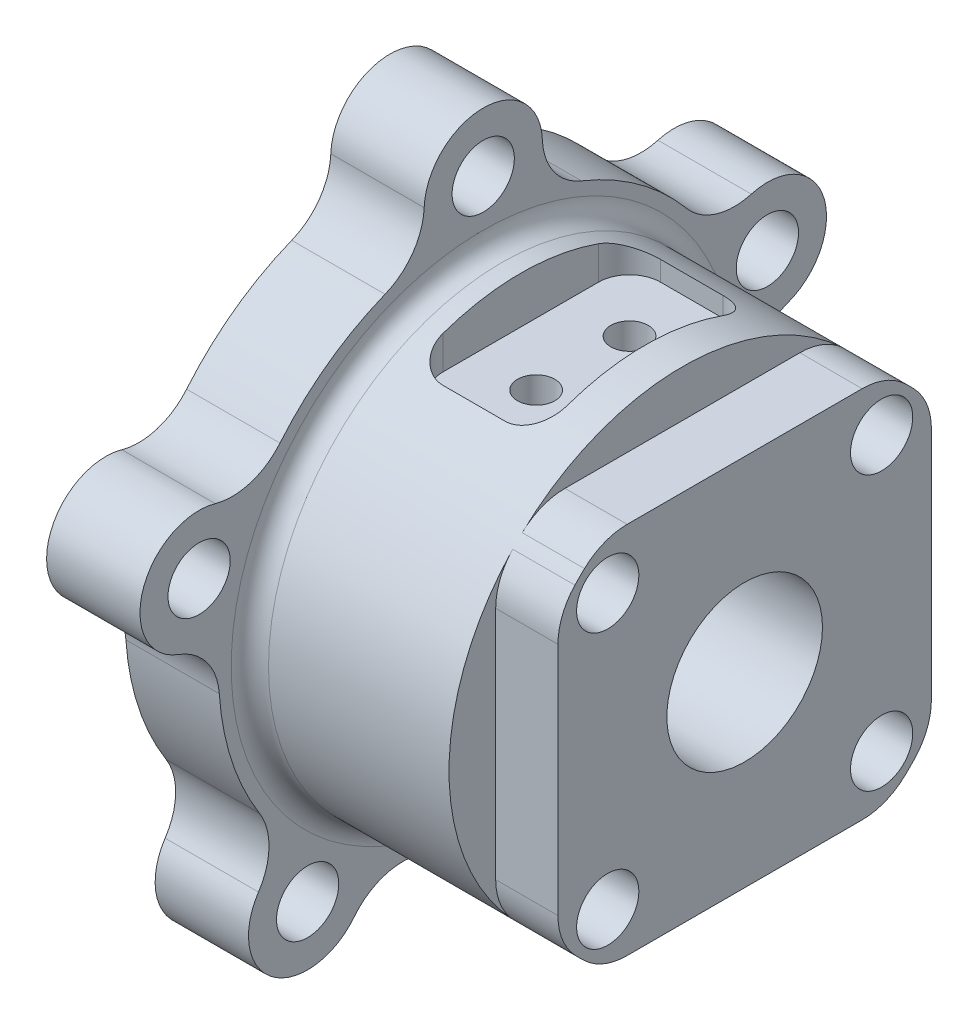
SolidWorks part; units mm, degrees
material "Plain Carbon Steel"
ref_plane "Front Plane" through (0, 0, 0) normal (0, 0, 1) x (1, 0, 0)
ref_plane "Top Plane" through (0, 0, 0) normal (0, 1, 0) x (1, 0, 0)
ref_plane "Right Plane" through (0, 0, 0) normal (1, 0, 0) x (0, 0, -1)
sketch "Sketch1" plane through (0, 0, 0) normal (0, 0, 1) x (1, 0, 0)
  line L0 (0, 0) -> (-104.2903, 0) construction
  line L1 (0, 0) -> (0, 37.5)
  line L2 (0, 37.5) -> (-42, 37.5)
  line L3 (-42, 37.5) -> (-42, 57.5)
  line L4 (-42, 57.5) -> (-57, 57.5)
  line L5 (-57, 57.5) -> (-57, 0)
  line L6 (-57, 0) -> (0, 0)
  dimension "D1" = 75
  dimension "D2" = 115
  dimension "D3" = 42
  dimension "D4" = 15
revolve "Revolve1" add sketch "Sketch1" angle 360 about L0
sketch "Sketch2" plane through (0, 0, 0) normal (1, 0, 0) x (0, 0, -1)
  line L1 (30, -30) -> (-30, -30)
  line L2 (30, -30) -> (30, 30)
  line L3 (30, 30) -> (-30, 30)
  line L4 (-30, -30) -> (-30, 30)
  line L5 (30, -30) -> (-30, 30) construction
  line L6 (30, 30) -> (-30, -30) construction
  circle A1 centre (0, 0) radius 48.1344
  point P0 (0, 0)
  dimension "D1" = 60
extrude "Cut-Extrude1" cut sketch "Sketch2" against normal blind 10
fillet "Fillet1" radius 10 8 edges at (-5, 30, 22.5) (-5, 30, -22.5) (-5, 22.5, -30) (-5, -22.5, -30) (-5, -30, -22.5) (-5, -30, 22.5) (-5, -22.5, 30) (-5, 22.5, 30)
hole_wizard "Ø10.0mm Dowel Hole2" positions "Sketch3" profile "Sketch4" hole size "Ø10.0" standard "ANSI Metric" end condition through all
sketch "Sketch3" plane through (0, 0, 0) normal (1, 0, 0) x (0, 0, -1)
  line L0 (30, -18.8746) -> (30, 18.8746) construction
  line L1 (-30, 18.8746) -> (-30, -18.8746) construction
  line L2 (18.8746, 30) -> (-18.8746, 30) construction
  line L3 (-18.8746, -30) -> (18.8746, -30) construction
  point P0 (22, 22)
  point P3 (-22, 22)
  point P6 (-22, -22)
  point P9 (22, -22)
  dimension "D1" = 8
  dimension "D2" = 8
  dimension "D3" = 8
  dimension "D4" = 8
sketch "Sketch4" plane through (0, 22, -22) normal (0, 1, 0) x (0, 0, -1)
  line L0 (0, 0) -> (0, 57)
  line L1 (0, 57) -> (5, 57)
  line L2 (5, 57) -> (5, 0)
  line L5 (5, 0) -> (0, 0)
  line L11 (0, -6.35) -> (0, 107.95) construction
  dimension "Thru Hole Dia." = 10
  dimension "Thru Hole Depth" = 57
sketch "Sketch5" plane through (0, 0, 0) normal (0, 1, 0) x (1, 0, 0)
  line L0 (0, 0) -> (-16, 0) construction
  line L1 (-36, 17.5) -> (-16, 17.5)
  line L2 (-36, 17.5) -> (-36, -17.5)
  line L3 (-36, -17.5) -> (-16, -17.5)
  line L4 (-16, 17.5) -> (-16, -17.5)
  line L5 (-10, -37.5) -> (-10, 37.5) construction
  line L6 (-42, -57.5) -> (-42, 57.5) construction
  dimension "D1" = 6
  dimension "D2" = 6
  dimension "D3" = 35
extrude "Cut-Extrude2" cut sketch "Sketch5" along normal through all from offset 30
fillet "Fillet2" radius 5 4 edges at (-16, 31.5831, 17.5) (-16, 31.5831, -17.5) (-36, 31.5831, 17.5) (-36, 31.5831, -17.5)
hole_wizard "Ø6.0mm Dowel Hole1" positions "Sketch6" profile "Sketch7" hole size "Ø6.0" standard "ANSI Metric"
sketch "Sketch6" plane through (0, 30, 0) normal (0, 1, 0) x (1, 0, 0)
  line L0 (0, 0) -> (-57, 0) construction
  line L1 (-57, 57.5) -> (-57, -57.5) construction
  line L2 (-26, 17.5) -> (-26, -17.5) construction
  line L3 (-31, 17.5) -> (-21, 17.5) construction
  line L4 (-21, -17.5) -> (-31, -17.5) construction
  point P0 (-26, 7.5)
  point P2 (-26, -7.5)
  dimension "D1" = 15
sketch "Sketch7" plane through (-26, 30, -7.5) normal (1, 0, 0) x (0, 0, 1)
  line L0 (0, 0) -> (0, 26.8026)
  line L1 (0, 26.8026) -> (3, 25)
  line L2 (3, 25) -> (3, 0)
  line L5 (3, 0) -> (0, 0)
  line L10 (0, 26.8026) -> (-3, 25) construction
  line L11 (0, -6.35) -> (0, 107.95) construction
  dimension "Hole Dia." = 6
  dimension "Hole Depth" = 25
  dimension "Drill Angle" = 118
hole_wizard "Ø10.0mm Dowel Hole1" positions "Sketch10" profile "Sketch9" hole size "Ø10.0" standard "ANSI Metric" end condition through all
sketch "Sketch10" plane through (-42, 0, 0) normal (1, 0, 0) x (0, 0, -1)
  point P0 (0, 48)
  dimension "D1" = 48
sketch "Sketch9" plane through (-42, 48, 0) normal (0, 1, 0) x (0, 0, -1)
  line L0 (0, 0) -> (0, 15)
  line L1 (0, 15) -> (5, 15)
  line L2 (5, 15) -> (5, 0)
  line L5 (5, 0) -> (0, 0)
  line L11 (0, -6.35) -> (0, 107.95) construction
  dimension "Thru Hole Dia." = 10
  dimension "Thru Hole Depth" = 15
pattern_circular "CirPattern1" count 5 over 360 about axis through (0, 0, 0) along (1, 0, 0) of "Ø10.0mm Dowel Hole1"
sketch "Sketch11" plane through (-42, 0, 0) normal (1, 0, 0) x (0, 0, -1)
  arc A0 (7.2618, 41.875) -> (-7.2618, 41.875) centre (0, 48) ccw
  circle A1 centre (0, 0) radius 57.5 construction
  arc A2 (-37.5815, 19.8465) -> (-42.0695, 6.0337) centre (-45.6507, 14.8328) ccw
  arc A3 (42.0695, 6.0337) -> (37.5815, 19.8465) centre (45.6507, 14.8328) ccw
  arc A4 (-30.4885, -29.6092) -> (-18.7386, -38.146) centre (-28.2137, -38.8328) ccw
  arc A5 (18.7386, -38.146) -> (30.4885, -29.6092) centre (28.2137, -38.8328) ccw
  arc A6 (-7.2618, 41.875) -> (-37.5815, 19.8465) centre (0, 0) ccw
  arc A7 (-42.0695, 6.0337) -> (-30.4885, -29.6092) centre (0, 0) ccw
  arc A8 (-18.7386, -38.146) -> (18.7386, -38.146) centre (0, 0) ccw
  arc A9 (30.4885, -29.6092) -> (42.0695, 6.0337) centre (0, 0) ccw
  arc A10 (37.5815, 19.8465) -> (7.2618, 41.875) centre (0, 0) ccw
  circle A11 centre (0, 0) radius 67.5
  dimension "D1" = 85
  dimension "D2" = 10
extrude "Cut-Extrude3" cut sketch "Sketch11" against normal through all
fillet "Fillet3" radius 10 10 edges at (-49.5, -38.146, 18.7386) (-49.5, -38.146, -18.7386) (-49.5, -29.6092, -30.4885) (-49.5, 6.0337, -42.0695) (-49.5, 19.8465, -37.5815) (-49.5, 41.875, -7.2618) (-49.5, 19.8465, 37.5815) (-49.5, 6.0337, 42.0695) (-49.5, -29.6092, 30.4885) (-49.5, 41.875, 7.2618)
hole_wizard "Ø25.0mm Dowel Hole1" positions "Sketch12" profile "Sketch14" hole size "Ø25.0" standard "ANSI Metric" end condition through all
sketch "Sketch12" plane through (0, 0, 0) normal (1, 0, 0) x (0, 0, -1)
  point P0 (0, 0)
sketch "Sketch14" plane through (0, 0, 0) normal (0, 1, 0) x (0, 0, -1)
  line L0 (0, 0) -> (0, 57)
  line L1 (0, 57) -> (12.5, 57)
  line L2 (12.5, 57) -> (12.5, 0)
  line L5 (12.5, 0) -> (0, 0)
  line L11 (0, -6.35) -> (0, 107.95) construction
  dimension "Thru Hole Dia." = 25
  dimension "Thru Hole Depth" = 57
fillet "Fillet4" radius 3 1 edges at (-42, 0, -37.5)
